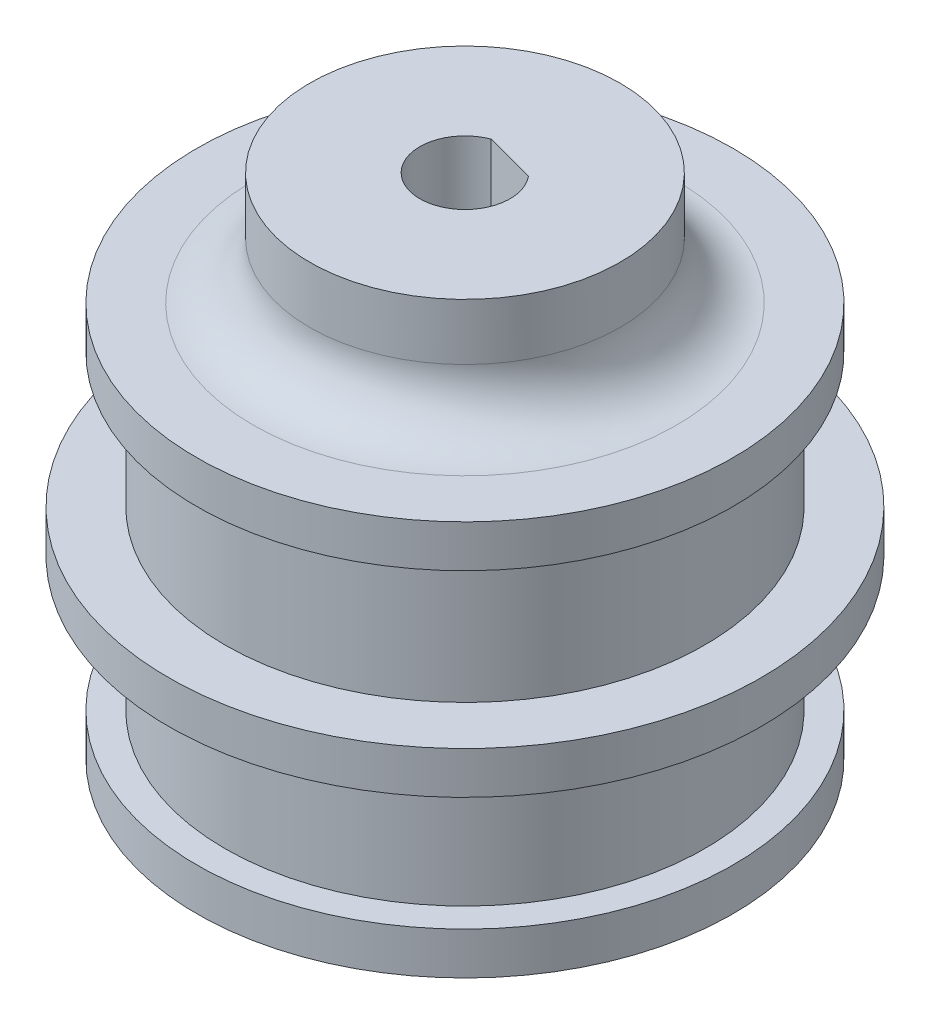
SolidWorks part; units mm, degrees
ref_plane "Płaszczyzna przednia" through (0, 0, 0) normal (0, 0, 1) x (1, 0, 0)
ref_plane "Płaszczyzna górna" through (0, 0, 0) normal (0, 1, 0) x (1, 0, 0)
ref_plane "Płaszczyzna prawa" through (0, 0, 0) normal (1, 0, 0) x (0, 0, -1)
sketch "Szkic1" plane through (0, 0, 0) normal (0, 0, 1) x (1, 0, 0)
  line L0 (0, -15.7831) -> (0, 15.7831) construction
  line L1 (7.5, -4.7992) -> (7.5, 0.2008)
  line L2 (7.5, -4.7992) -> (9.5, -4.7992)
  line L3 (9.5, -4.7992) -> (9.5, -3.2992)
  line L4 (9.5, -3.2992) -> (8.5, -3.2992)
  line L5 (8.5, -3.2992) -> (8.5, 1.4508)
  line L6 (8.5, 1.4508) -> (10.5, 1.4508)
  line L7 (10.5, 1.4508) -> (10.5, 2.9508)
  line L8 (10.5, 2.9508) -> (8.5, 2.9508)
  line L9 (8.5, 2.9508) -> (8.5, 7.7008)
  line L10 (8.5, 7.7008) -> (9.5, 7.7008)
  line L11 (9.5, 7.7008) -> (9.5, 9.2008)
  line L12 (9.5, 9.2008) -> (5.5, 9.2008)
  line L13 (5.5, 9.2008) -> (5.5, 13.2008)
  line L14 (5.5, 13.2008) -> (0, 13.2008)
  line L15 (3.5, 4.2008) -> (0, 4.2008)
  line L16 (0, 13.2008) -> (0, 4.2008)
  arc A0 (7.5, 0.2008) -> (3.5, 4.2008) centre (3.5, 0.2008) ccw
  point P21 (7.5, 4.2008)
  dimension "D16" = 4
  dimension "D1" = 7.5
  dimension "D2" = 9
  dimension "D3" = 2
  dimension "D4" = 1.5
  dimension "D5" = 1.5
  dimension "D6" = 2
  dimension "D7" = 2
  dimension "D8" = 8.5
  dimension "D9" = 8.5
  dimension "D10" = 1
  dimension "D11" = 14
  dimension "D12" = 1.5
  dimension "D13" = 9
  dimension "D14" = 4
  dimension "D15" = 4
revolve "Obrót1" add sketch "Szkic1" angle 360 about L0
fillet "Zaokrąglenie1" radius 2 1 edges at (0, 9.2008, -5.5)
sketch "Szkic2" plane through (0, 13.2008, 0) normal (0, 1, 0) x (1, 0, 0)
  line L0 (-0.5627, 1.3904) -> (1.1773, 0.9295) construction
  line L2 (-0.5688, 1.4955) -> (1.2345, 1.0178)
  circle A0 centre (0, 0) radius 1.5 construction
  arc A3 (1.2345, 1.0178) -> (-0.5688, 1.4955) centre (0, 0) cw
  dimension "D1" = 3
  dimension "D2" = 1.2
extrude "Wytnij-wyciągnięcie1" cut sketch "Szkic2" against normal through all
